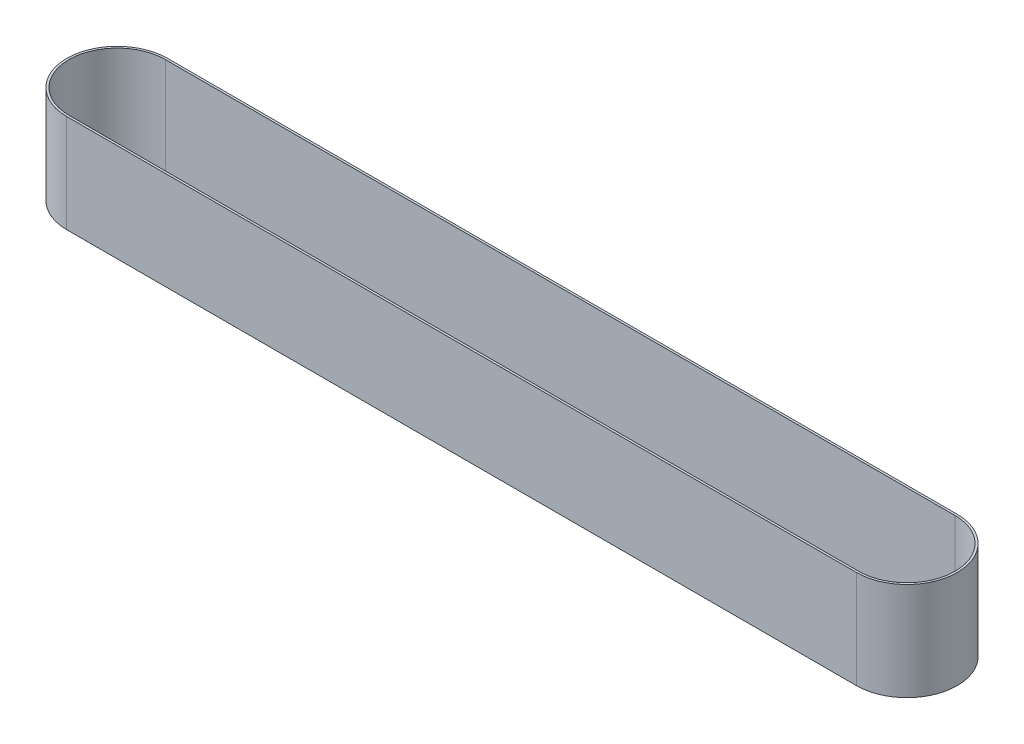
SolidWorks part; units mm, degrees
ref_plane "Front Plane" through (0, 0, 0) normal (0, 0, 1) x (1, 0, 0)
ref_plane "Top Plane" through (0, 0, 0) normal (0, 1, 0) x (1, 0, 0)
ref_plane "Right Plane" through (0, 0, 0) normal (1, 0, 0) x (0, 0, -1)
sketch "Sketch1" plane through (0, 0, 0) normal (0, 1, 0) x (1, 0, 0)
  line L0 (0, 0) -> (368.3, 0) construction
  line L1 (0, 23.5) -> (368.3, 23.5)
  line L2 (0, -23.5) -> (368.3, -23.5)
  line L3 (0, 0) -> (368.3, 0) construction
  line L4 (0, 22.5) -> (368.3, 22.5)
  line L5 (0, -22.5) -> (368.3, -22.5)
  arc A0 (0, 23.5) -> (0, -23.5) centre (0, 0) ccw
  arc A1 (368.3, -23.5) -> (368.3, 23.5) centre (368.3, 0) ccw
  arc A2 (0, 22.5) -> (0, -22.5) centre (0, 0) ccw
  arc A3 (368.3, -22.5) -> (368.3, 22.5) centre (368.3, 0) ccw
  point P3 (184.15, 0)
  point P10 (184.15, 0)
  dimension "D1" = 368.3
extrude "Boss-Extrude1" add sketch "Sketch1" along normal blind 45.72
